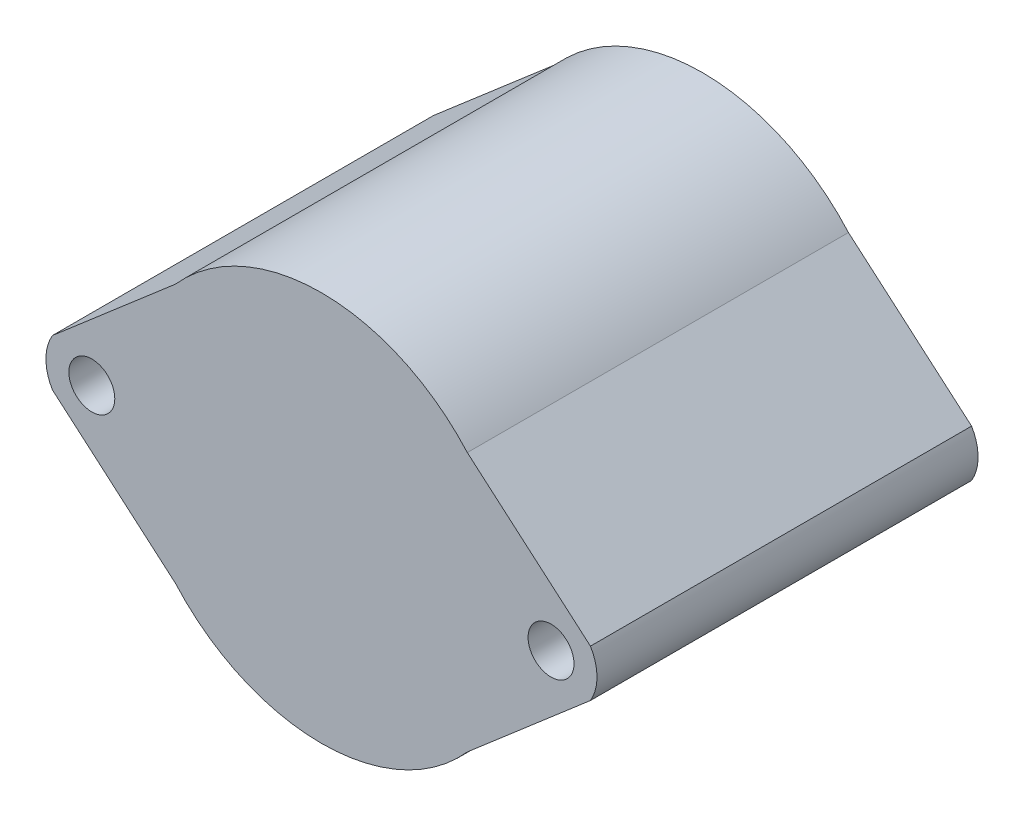
SolidWorks part; units mm, degrees
ref_plane "Front Plane" through (0, 0, 0) normal (0, 0, 1) x (1, 0, 0)
ref_plane "Top Plane" through (0, 0, 0) normal (0, 1, 0) x (1, 0, 0)
ref_plane "Right Plane" through (0, 0, 0) normal (1, 0, 0) x (0, 0, -1)
sketch "Sketch2" plane through (0, 0, 0) normal (0, 0, 1) x (1, 0, 0)
  line L4 (23.4338, 2.0516) -> (12.7089, 11.2908)
  line L5 (23.4338, -2.0516) -> (12.7089, -11.2908)
  line L6 (-23.4338, -2.0516) -> (-12.7089, -11.2908)
  line L7 (-23.4338, 2.0516) -> (-12.7089, 11.2908)
  arc A6 (23.4338, -2.0516) -> (23.4338, 2.0516) centre (20, 0) ccw
  arc A7 (-12.7089, -11.2908) -> (12.7089, -11.2908) centre (0, 0) ccw
  arc A8 (-23.4338, 2.0516) -> (-23.4338, -2.0516) centre (-20, 0) ccw
  arc A9 (12.7089, 11.2908) -> (-12.7089, 11.2908) centre (0, 0) ccw
  circle A10 centre (-20, 0) radius 2
  circle A11 centre (20, 0) radius 2
extrude "Boss-Extrude2" add sketch "Sketch2" along normal blind 33.2
